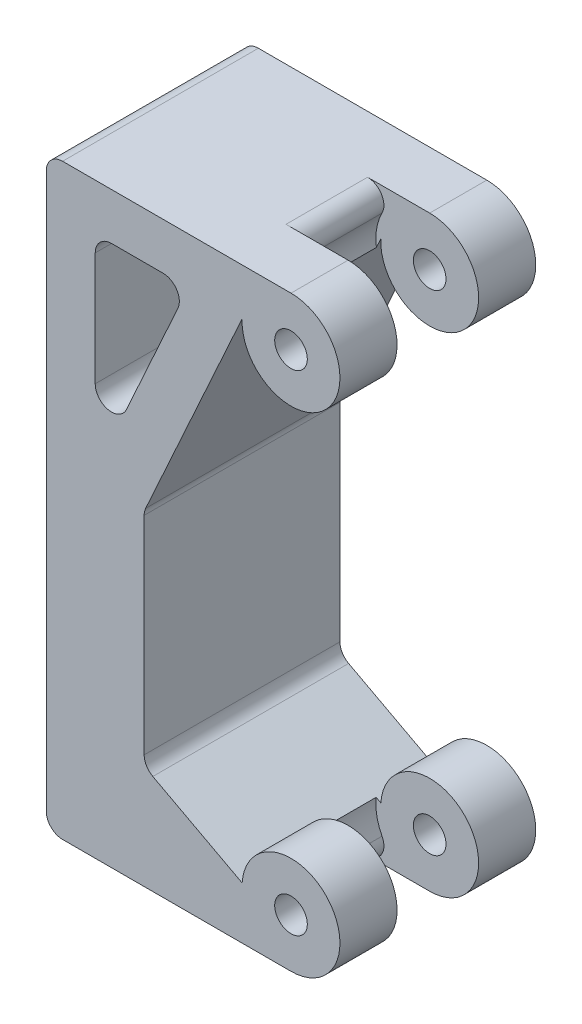
SolidWorks part; units mm, degrees
ref_plane "Front Plane" through (0, 0, 0) normal (0, 0, 1) x (1, 0, 0)
ref_plane "Top Plane" through (0, 0, 0) normal (0, 1, 0) x (1, 0, 0)
ref_plane "Right Plane" through (0, 0, 0) normal (1, 0, 0) x (0, 0, -1)
sketch "Sketch1" plane through (0, 0, 0) normal (0, 0, 1) x (1, 0, 0)
  line L0 (0, 0) -> (15, 0)
  line L2 (0, 0) -> (0, 36)
  line L3 (0, 36) -> (15, 36)
  line L5 (12.0031, 33.1373) -> (6, 19.9206)
  line L6 (6, 19.9206) -> (6, 6.3916)
  line L7 (6, 6.3916) -> (12.0064, 3.1954)
  line L11 (15, 33) -> (15, 3) construction
  line L12 (8.7082, 33.1373) -> (3, 33.1373)
  line L13 (3, 33.1373) -> (3, 20.57)
  line L14 (3, 20.57) -> (8.7082, 33.1373)
  arc A0 (15, 0) -> (12.0064, 3.1954) centre (15, 3) ccw
  arc A1 (15, 36) -> (12.0031, 33.1373) centre (15, 33) cw
  circle A2 centre (15, 33) radius 1
  circle A3 centre (15, 3) radius 1
  dimension "D1" = 2
  dimension "D3" = 3
  dimension "D2" = 6
  dimension "D4" = 30
  dimension "D5" = 15
  dimension "D6" = 3
  dimension "D7" = 3
extrude "Boss-Extrude1" add sketch "Sketch1" along normal blind 12
ref_plane "midplane" through (0, 0, 6) normal (0, 0, 1) x (1, 0, 0)
sketch "Sketch2" plane through (0, 0, 6) normal (0, 0, 1) x (1, 0, 0)
  circle A0 centre (15, 33) radius 3.3
  circle A1 centre (15, 3) radius 3.3
  dimension "D1" = 6.6
extrude "Cut-Extrude1" cut sketch "Sketch2" against normal blind 2.5 and the other way blind 2.5
fillet "Fillet1" radius 1 2 edges at (0, 0, 6) (0, 36, 6)
fillet "Fillet2" radius 1 2 edges at (6, 6.3916, 6) (6, 19.9206, 6)
fillet "Fillet3" radius 1 2 edges at (13.6252, 36, 6) (13.6252, 0, 6)
fillet "Fillet4" radius 1 3 edges at (3, 20.57, 6) (8.7082, 33.1373, 6) (3, 33.1373, 6)
equation "\"axle-diameter\"=2"
equation "\"D1@Sketch1\"=\"axle-diameter\""
equation "\"switch-thickness\"=12"
equation "\"D1@Boss-Extrude1\"=\"switch-thickness\""
equation "\"base-width\"=6"
equation "\"D2@Sketch1\"=\"base-width\""
equation "\"axle-bushing-radius\"=3"
equation "\"D3@Sketch1\"= \"axle-bushing-radius\""
equation "\"D1@Sketch2\"=\"axle-bushing-radius\"*2.2"
equation "\"D1@Cut-Extrude1\"=\"switch-thickness\"/6+\"clearance\""
equation "\"D2@Cut-Extrude1\"=\"switch-thickness\"/6+\"clearance\""
equation "\"clearance\"= 0.5"
